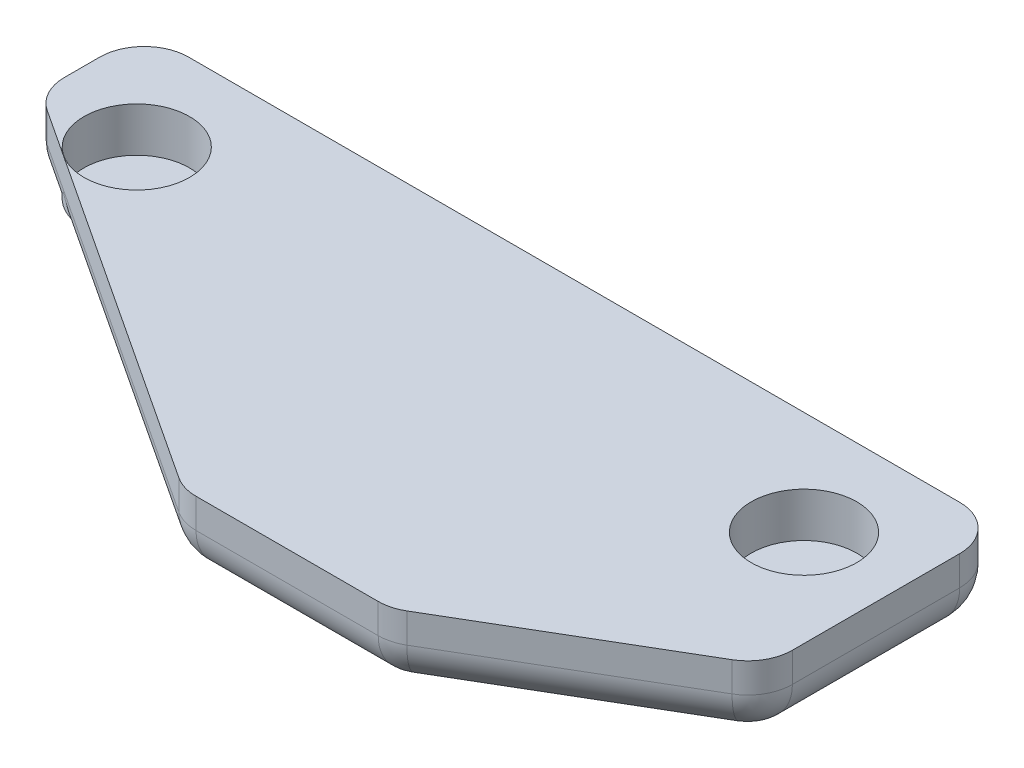
SolidWorks part; units mm, degrees
ref_plane "Front Plane" through (0, 0, 0) normal (0, 0, 1) x (1, 0, 0)
ref_plane "Top Plane" through (0, 0, 0) normal (0, 1, 0) x (1, 0, 0)
ref_plane "Right Plane" through (0, 0, 0) normal (1, 0, 0) x (0, 0, -1)
sketch "Sketch2" plane through (0, 0, 0) normal (0, 1, 0) x (1, 0, 0)
  line L0 (-21.2162, 11.7419) -> (-21.2162, 8.2419)
  line L1 (-21.2162, 8.2419) -> (-7.2162, -0.9581)
  line L2 (-7.2162, -0.9581) -> (-0.2162, -0.9581)
  line L3 (-0.2162, -0.9581) -> (7.7838, 3.7419)
  line L4 (7.7838, 3.7419) -> (7.7838, 11.7419)
  line L7 (-21.2162, 11.7419) -> (7.7838, 11.7419)
  dimension "D1" = 29
  dimension "D2" = 12.7
  dimension "D3" = 8
  dimension "D4" = 8
  dimension "D5" = 3.5
  dimension "D6" = 7
extrude "Boss-Extrude1" add sketch "Sketch2" along normal blind 2.5
sketch "Sketch4" plane through (0, 2.5, 0) normal (0, 1, 0) x (1, 0, 0)
  line L0 (-17.9662, 11.241) -> (-17.9662, -1.2869) construction
  line L1 (-21.2162, 8.2419) -> (7.7838, 8.2419) construction
  line L2 (-21.2162, 11.7419) -> (-21.2162, 8.2419) construction
  line L3 (7.7838, 11.7419) -> (-21.2162, 11.7419) construction
  line L4 (-6.7162, 11.7419) -> (-6.7162, -0.9581) construction
  line L5 (-7.2162, -0.9581) -> (-0.2162, -0.9581) construction
  line L6 (4.5338, 11.241) -> (4.5338, -1.2869) construction
  circle A0 centre (-17.9662, 8.2419) radius 1.78
  circle A1 centre (4.5338, 8.2419) radius 1.78
  point P15 (-6.7162, 8.2419)
  dimension "D1" = 3.25
  dimension "D2" = 3.5
extrude "Cut-Extrude1" cut sketch "Sketch4" against normal blind 1.5
fillet "Fillet1" radius 1.5 12 edges at (-0.2162, 1.25, 0.9581) (-7.2162, 1.25, 0.9581) (-21.2162, 0, -9.9919) (-14.2162, 0, -3.6419) (-3.7162, 0, 0.9581) (3.7838, 0, -1.3919) (7.7838, 1.25, -3.7419) (7.7838, 0, -7.7419) (-6.7162, 0, -11.7419) (7.7838, 1.25, -11.7419) (-21.2162, 1.25, -8.2419) (-21.2162, 1.25, -11.7419)
